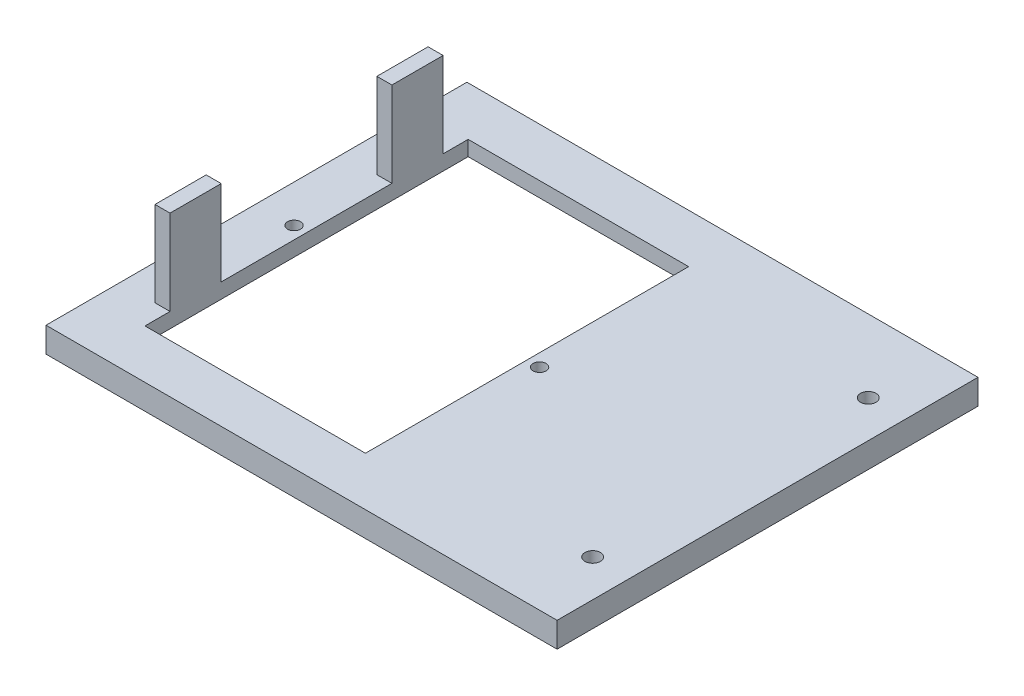
SolidWorks part; units mm, degrees
ref_plane "Front Plane" through (0, 0, 0) normal (0, 0, 1) x (1, 0, 0)
ref_plane "Top Plane" through (0, 0, 0) normal (0, 1, 0) x (1, 0, 0)
ref_plane "Right Plane" through (0, 0, 0) normal (1, 0, 0) x (0, 0, -1)
sketch "Sketch1" plane through (0, 0, 0) normal (0, 1, 0) x (1, 0, 0)
  line L1 (-55, 42) -> (55, 42)
  line L2 (-55, 42) -> (-55, -42)
  line L3 (-55, -42) -> (55, -42)
  line L4 (55, 42) -> (55, -42)
  line L5 (-55, 42) -> (55, -42) construction
  line L6 (-55, -42) -> (55, 42) construction
  point P0 (0, 0)
  dimension "D1" = 110
  dimension "D2" = 84
extrude "Boss-Extrude1" add sketch "Sketch1" along normal blind 5
sketch "Sketch2" plane through (0, 5, 0) normal (0, 1, 0) x (1, 0, 0)
  line L0 (-55, 42) -> (-55, -42) construction
  line L1 (-45, 32.25) -> (-1, 32.25)
  line L2 (-45, 32.25) -> (-45, -32.25)
  line L3 (-45, -32.25) -> (-1, -32.25)
  line L4 (-1, 32.25) -> (-1, -32.25)
  line L5 (-45, 32.25) -> (-1, -32.25) construction
  line L6 (-45, -32.25) -> (-1, 32.25) construction
  line L7 (-55, -42) -> (55, -42) construction
  point P0 (-23, 0)
  dimension "D1" = 64.5
  dimension "D2" = 44
  dimension "D3" = 10
  dimension "D4" = 9.75
extrude "Cut-Extrude1" cut sketch "Sketch2" against normal blind 5
sketch "Sketch3" plane through (0, 5, 0) normal (0, 1, 0) x (1, 0, 0)
  line L0 (0, 0) -> (69.4971, 0)
  line L1 (-45, 32.25) -> (-45, -32.25) construction
  circle A0 centre (39.6, 27.5) radius 1.55
  circle A1 centre (39.6, -27.5) radius 1.55
  dimension "D1" = 3.1
  dimension "D2" = 84.6
  dimension "D3" = 27.5
extrude "Cut-Extrude2" cut sketch "Sketch3" against normal blind 5 contours A1 | A0
sketch "Sketch5" plane through (0, 5, 0) normal (0, 1, 0) x (1, 0, 0)
  line L0 (-45, 32.25) -> (-45, -32.25) construction
  line L1 (-45, 27.25) -> (-48, 27.25)
  line L2 (-45, 27.25) -> (-45, 17.0364)
  line L3 (-45, 17.0364) -> (-48, 17.0364)
  line L4 (-48, 27.25) -> (-48, 17.0364)
  line L5 (-1, 32.25) -> (-45, 32.25) construction
  line L6 (0, 0) -> (-31.529, 0)
  line L7 (-45, -17.0364) -> (-48, -17.0364)
  line L8 (-48, -27.25) -> (-48, -17.0364)
  line L9 (-45, -27.25) -> (-48, -27.25)
  line L10 (-45, -27.25) -> (-45, -17.0364)
  line M12 (-45, -32.25) -> (-45, 32.25)
  dimension "D1" = 5
  dimension "D2" = 3
extrude "Boss-Extrude2" add sketch "Sketch5" along normal blind 17 contours L1 L4 L3 M12 | L9 L7 L8 M12
sketch "Sketch6" plane through (0, 0, 0) normal (0, -1, 0) x (1, 0, 0)
  line L0 (-45, 32.25) -> (-1, 32.25) construction
  line L1 (4, 37.25) -> (-50, 37.25)
  line L2 (4, 37.25) -> (4, -37.25)
  line L3 (4, -37.25) -> (-50, -37.25)
  line L4 (-50, 37.25) -> (-50, -37.25)
  line L5 (-1, 32.25) -> (-1, -32.25) construction
  line L6 (-45, -32.25) -> (-45, 32.25) construction
  line L7 (-1, -32.25) -> (-45, -32.25) construction
  dimension "D1" = 5
  dimension "D2" = 5
  dimension "D3" = 5
  dimension "D4" = 5
extrude "Cut-Extrude3" cut sketch "Sketch6" against normal blind 2
sketch "Sketch7" plane through (0, 2, 0) normal (0, -1, 0) x (1, 0, 0)
  line L0 (-45, 32.25) -> (-45, -32.25) construction
  line L1 (-1, -32.25) -> (-1, 32.25) construction
  circle A0 centre (-47.5, 0) radius 1.3
  circle A1 centre (1.5, 0) radius 1.3
  dimension "D1" = 2.6
  dimension "D2" = 2.6
  dimension "D3" = 2.5
  dimension "D4" = 2.5
extrude "Cut-Extrude4" cut sketch "Sketch7" against normal up to next
sketch "Sketch8" plane through (55, 0, 0) normal (1, 0, 0) x (0, 0, -1)
  line L1 (-42, 5) -> (42, 5)
  line L2 (-42, 5) -> (-42, 0)
  line L3 (-42, 0) -> (42, 0)
  line L4 (42, 5) -> (42, 0)
extrude "Cut-Extrude5" cut sketch "Sketch8" against normal blind 8
